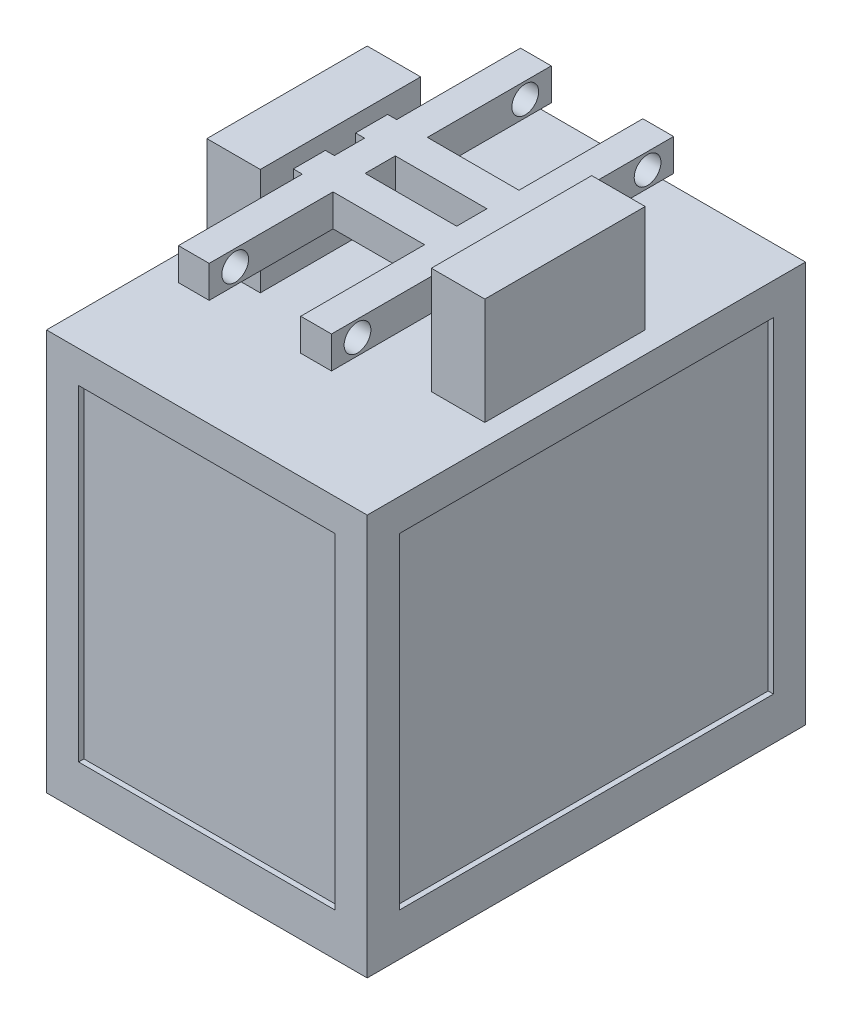
SolidWorks part; units mm, degrees
material "Cast Alloy Steel"
ref_plane "Front Plane" through (0, 0, 0) normal (0, 0, 1) x (1, 0, 0)
ref_plane "Top Plane" through (0, 0, 0) normal (0, 1, 0) x (1, 0, 0)
ref_plane "Right Plane" through (0, 0, 0) normal (1, 0, 0) x (0, 0, -1)
sketch "Sketch2" plane through (0, 0, 0) normal (0, 1, 0) x (1, 0, 0)
  line L1 (-240, 350) -> (240, 350)
  line L2 (-240, 350) -> (-240, -350)
  line L3 (-240, -350) -> (240, -350)
  line L4 (240, 350) -> (240, -350)
  line L5 (-240, 350) -> (240, -350) construction
  line L6 (-240, -350) -> (240, 350) construction
  point P0 (0, 0)
  dimension "D1" = 480
  dimension "D2" = 700
extrude "Boss-Extrude1" add sketch "Sketch2" along normal blind 60
sketch "Sketch3" plane through (0, 0, 0) normal (0, 1, 0) x (1, 0, 0)
  line L0 (240, -350) -> (240, 350) construction
  line L1 (-300, 410) -> (300, 410)
  line L2 (-300, 410) -> (-300, -410)
  line L3 (-300, -410) -> (300, -410)
  line L4 (300, 410) -> (300, -410)
  line L5 (-300, 410) -> (300, -410) construction
  line L6 (-300, -410) -> (300, 410) construction
  line L7 (240, 350) -> (-240, 350) construction
  line L9 (-240, 350) -> (240, 350)
  line L10 (-240, 350) -> (-240, -350)
  line L11 (-240, -350) -> (240, -350)
  line L12 (240, 350) -> (240, -350)
  line L13 (-240, 350) -> (240, -350) construction
  line L14 (-240, -350) -> (240, 350) construction
  line L18 (240, -350) -> (240, 350)
  line L19 (-240, -350) -> (240, -350)
  line L20 (-240, 350) -> (-240, -350)
  line L21 (240, 350) -> (-240, 350)
  line L22 (240, -350) -> (240, 350)
  line L23 (-240, -350) -> (240, -350)
  line L24 (-240, 350) -> (-240, -350)
  line L25 (240, 350) -> (-240, 350)
  point P0 (0, 0)
  point P10 (0, 0)
  dimension "D1" = 60
  dimension "D2" = 60
  dimension "D3" = 0
  dimension "D4" = 600
  dimension "D5" = 820
extrude "Boss-Extrude4" add sketch "Sketch3" along normal blind 80 contours L4 L1 L2 L3 L9 L12 L11 L10
sketch "Sketch5" plane through (0, 80, 0) normal (0, 1, 0) x (1, 0, 0)
  line L0 (240, 410) -> (240, 350)
  line L1 (-300, 410) -> (-240, 410)
  line L2 (-300, 410) -> (-300, 350)
  line L3 (-300, 350) -> (-240, 350)
  line L4 (-240, 410) -> (-240, 350)
  line L5 (240, 410) -> (300, 410)
  line L6 (300, 410) -> (300, 350)
  line L7 (240, 350) -> (300, 350)
  line L8 (240, -350) -> (240, -410)
  line L9 (240, -350) -> (300, -350)
  line L10 (300, -350) -> (300, -410)
  line L11 (240, -410) -> (300, -410)
  line L12 (-300, -350) -> (-300, -410)
  line L13 (-300, -350) -> (-240, -350)
  line L14 (-240, -350) -> (-240, -410)
  line L15 (-300, -410) -> (-240, -410)
  line L16 (-300, -410) -> (300, -410) construction
  line L17 (300, 410) -> (300, -410) construction
  dimension "D1" = 2
  dimension "D2" = 2
  dimension "D3" = 60
  dimension "D4" = 60
  dimension "D5" = 60
extrude "Boss-Extrude5" add sketch "Sketch5" along normal blind 610
ref_plane "Plane1" through (0, 690, 0) normal (0, 1, 0) x (1, 0, 0)
sketch "Sketch7" plane through (0, 690, 0) normal (0, 1, 0) x (1, 0, 0)
  line L1 (-300, 410) -> (300, 410)
  line L2 (-300, 410) -> (-300, -410)
  line L3 (-300, -410) -> (300, -410)
  line L4 (300, 410) -> (300, -410)
extrude "Boss-Extrude6" add sketch "Sketch7" along normal blind 60
sketch "Sketch10" plane through (0, 80, 0) normal (0, 1, 0) x (1, 0, 0)
  line L6 (270, -380) -> (-270, -380)
  line L8 (290, 380) -> (290, -400)
  line L12 (270, 380) -> (270, -380)
  line L16 (300, -410) -> (300, 410) construction
  line L17 (-290, -400) -> (290, -400)
  line L20 (0, 0) -> (0, -136.5674) construction
  line L21 (-290, 380) -> (-290, -400)
  line L22 (-270, 380) -> (-270, -380)
  line L23 (290, 380) -> (270, 380)
  line L24 (-270, 380) -> (-290, 380)
  point P0 (0, 0)
  dimension "D1" = 30
  dimension "D7" = 10
extrude "Boss-Extrude7" add sketch "Sketch10" along normal up to surface (670 mm away) up to face at (0, 750, 0)
ref_plane "Plane3" through (0, 20, 0) normal (0, -1, 0) x (-1, 0, 0)
ref_plane "Plane4" through (0, 730, 0) normal (0, 1, 0) x (1, 0, 0)
sketch "Sketch21" plane through (0, 750, 0) normal (0, 1, 0) x (1, 0, 0)
  line L0 (0, 410) -> (0, 340) construction
  line L1 (300, 410) -> (-300, 410) construction
  line L2 (-300, 0) -> (300, 0) construction
  line L3 (-300, 410) -> (-300, -410) construction
  line L4 (300, -410) -> (300, 410) construction
  line L10 (0, 0) -> (0, 240) construction
  line L11 (0, -290) -> (0, -302.4798) construction
  line L18 (260, -150) -> (160, 150) construction
  line L19 (-260, 150) -> (-160, 150)
  line L20 (-260, 150) -> (-260, -150)
  line L21 (-260, -150) -> (-160, -150)
  line L22 (-160, 150) -> (-160, -150)
  line L23 (-260, 150) -> (-160, -150) construction
  line L24 (-260, -150) -> (-160, 150) construction
  line L25 (260, 150) -> (160, -150) construction
  line L26 (160, 150) -> (160, -150)
  line L27 (260, -150) -> (160, -150)
  line L28 (260, 150) -> (260, -150)
  line L29 (260, 150) -> (160, 150)
  line L30 (0, 240) -> (0, 0) construction
  line L31 (0, -302.4798) -> (0, -290) construction
  point P11 (0, 290)
  point P22 (0, -290)
  point P23 (-210, 0)
  point P32 (210, 0)
  dimension "D4" = 300
  dimension "D5" = 100
  dimension "D6" = 40
extrude "Boss-Extrude13" add sketch "Sketch21" along normal blind 200
sketch "Sketch28" plane through (260, 0, 0) normal (1, 0, 0) x (0, 0, -1)
  line L0 (0, 950) -> (0, 750) construction
  line L1 (-150, 950) -> (150, 950) construction
  line L2 (-150, 750) -> (150, 750) construction
  line L3 (88.2623, 860) -> (28.2623, 860)
  line L4 (-88.2623, 920) -> (-28.2623, 920)
  line L5 (-88.2623, 920) -> (-88.2623, 860)
  line L6 (-88.2623, 860) -> (-28.2623, 860)
  line L7 (-28.2623, 920) -> (-28.2623, 860)
  line L8 (88.2623, 920) -> (88.2623, 860)
  line L9 (88.2623, 920) -> (28.2623, 920)
  line L10 (28.2623, 920) -> (28.2623, 860)
  dimension "D1" = 60
  dimension "D2" = 60
  dimension "D3" = 56.5245
  dimension "D4" = 110
extrude "Boss-Extrude18" add sketch "Sketch28" against normal up to surface (520 mm away) up to face at (-260, 850, 0)
sketch "Sketch29" plane through (0, 0, 0) normal (0, 0, 1) x (1, 0, 0)
  line L0 (-160, 890) -> (160, 890) construction
  line L1 (-160, 860) -> (-160, 920) construction
  line L2 (160, 920) -> (160, 860) construction
  line L3 (-160, 860) -> (160, 860) construction
  line L4 (-143.181, 920) -> (-85.6471, 920)
  line L5 (-143.181, 920) -> (-143.181, 860)
  line L6 (-143.181, 860) -> (-85.6471, 860)
  line L7 (-85.6471, 920) -> (-85.6471, 860)
  line L8 (-143.181, 920) -> (-85.6471, 860) construction
  line L9 (-143.181, 860) -> (-85.6471, 920) construction
  line L10 (0, 920) -> (0, 860) construction
  line L11 (-160, 920) -> (160, 920) construction
  line L12 (143.181, 860) -> (85.6471, 920) construction
  line L13 (143.181, 920) -> (85.6471, 860) construction
  line L14 (85.6471, 920) -> (85.6471, 860)
  line L15 (143.181, 860) -> (85.6471, 860)
  line L16 (143.181, 920) -> (143.181, 860)
  line L17 (143.181, 920) -> (85.6471, 920)
  point P6 (-114.4141, 890)
  point P22 (114.4141, 890)
extrude "Boss-Extrude19" add sketch "Sketch29" along normal mid plane 640
sketch "Sketch30" plane through (0, 0, 0) normal (1, 0, 0) x (0, 0, -1)
  line L0 (-320, 890) -> (320, 890) construction
  line L1 (-320, 860) -> (-320, 920) construction
  line L2 (320, 860) -> (320, 920) construction
  line L3 (0, 950) -> (0, 750) construction
  line L4 (-150, 950) -> (150, 950) construction
  line L5 (-410, 750) -> (410, 750) construction
  circle A0 centre (-271.3248, 890) radius 25
  circle A1 centre (271.3248, 890) radius 25
  dimension "D1" = 50
extrude "Cut-Extrude1" cut sketch "Sketch30" against normal mid plane 640
